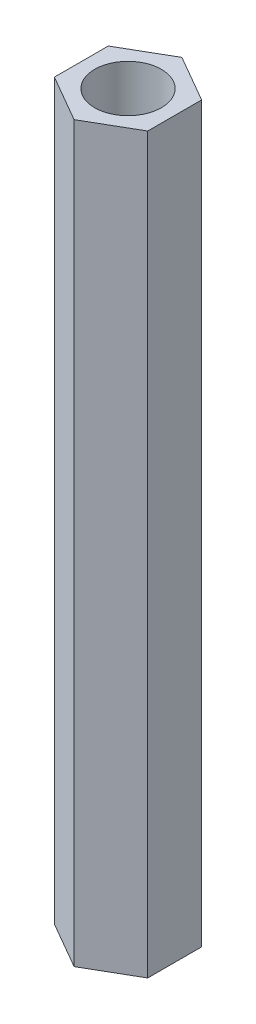
SolidWorks part; units mm, degrees
ref_plane "前视基准面" through (0, 0, 0) normal (0, 0, 1) x (1, 0, 0)
ref_plane "上视基准面" through (0, 0, 0) normal (0, 1, 0) x (1, 0, 0)
ref_plane "右视基准面" through (0, 0, 0) normal (1, 0, 0) x (0, 0, -1)
sketch "草图1" plane through (0, 0, 0) normal (0, 1, 0) x (1, 0, 0)
  line L0 (0, 0) -> (0, 4.0415) construction
  line L1 (0, 4.0415) -> (-3.5, 2.0207)
  line L2 (-3.5, 2.0207) -> (-3.5, -2.0207)
  line L3 (-3.5, -2.0207) -> (0, -4.0415)
  line L4 (0, -4.0415) -> (3.5, -2.0207)
  line L5 (3.5, -2.0207) -> (3.5, 2.0207)
  line L6 (3.5, 2.0207) -> (0, 4.0415)
  circle A0 centre (0, 0) radius 2.5
  circle A1 centre (0, 0) radius 3.5 construction
  dimension "D2" = 5
  dimension "D1" = 7
extrude "凸台-拉伸1" add sketch "草图1" along normal blind 55
